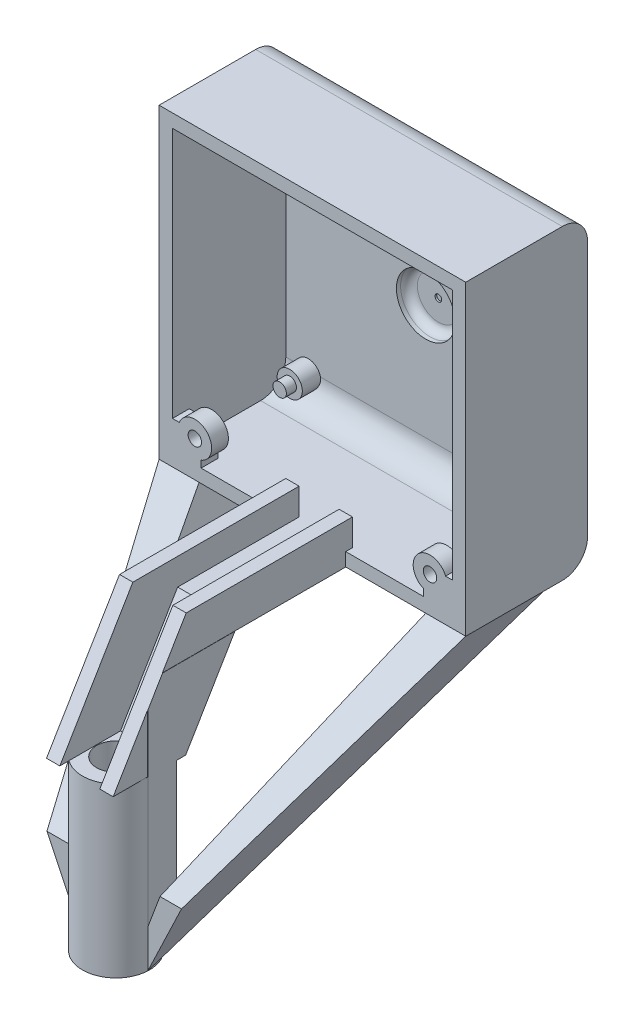
SolidWorks part; units mm, degrees
ref_plane "Front Plane" through (0, 0, 0) normal (0, 0, 1) x (1, 0, 0)
ref_plane "Top Plane" through (0, 0, 0) normal (0, 1, 0) x (1, 0, 0)
ref_plane "Right Plane" through (0, 0, 0) normal (1, 0, 0) x (0, 0, -1)
sketch "Sketch1" plane through (0, 0, 0) normal (0, 0, 1) x (1, 0, 0)
  line L0 (0, 0) -> (0, -36.5125)
  line L1 (0, -36.5125) -> (36.5125, -36.5125)
  line L2 (36.5125, -36.5125) -> (36.5125, 0)
  line L3 (36.5125, 0) -> (0, 0)
  dimension "D1" = 36.5125
extrude "Extrude1" add sketch "Sketch1" along normal blind 1
sketch "Sketch2" plane through (0, 0, 1) normal (0, 0, 1) x (1, 0, 0)
  line L0 (1.5875, -1.5875) -> (34.925, -1.5875)
  line L3 (34.925, -34.925) -> (34.925, -1.5875)
  line L4 (1.5875, -34.925) -> (1.5875, -1.5875)
  line L5 (34.925, -34.925) -> (1.5875, -34.925)
  line L6 (0, 0) -> (36.5125, 0)
  line L7 (36.5125, -36.5125) -> (36.5125, 0) construction
  line L8 (36.5125, 0) -> (0, 0) construction
  line L9 (36.5125, 0) -> (36.5125, -36.5125)
  line L10 (0, -36.5125) -> (36.5125, -36.5125) construction
  line L11 (36.5125, -36.5125) -> (0, -36.5125)
  line L12 (0, 0) -> (0, -36.5125) construction
  line L13 (0, -36.5125) -> (0, 0)
extrude "Extrude2" add sketch "Sketch2" along normal blind 13.5
fillet "Fillet7" radius 3 4 edges at (18.2562, 0, 0) (18.2562, -36.5125, 0) (18.2562, -1.5875, 1) (18.2562, -34.925, 1)
sketch "Sketch5" plane through (0, 0, 1) normal (0, 0, 1) x (1, 0, 0)
  line L0 (1.5875, -1.5875) -> (34.925, -34.925) construction
  line L1 (34.925, -1.5875) -> (1.5875, -34.925) construction
  line L2 (34.925, -34.925) -> (34.925, -1.5875) construction
  circle A0 centre (4.2562, -4.2562) radius 1.5
  circle A1 centre (32.2563, -4.2562) radius 1.5
  circle A2 centre (4.2562, -32.2563) radius 1.5
  circle A3 centre (32.2563, -32.2563) radius 1.5
  point P8 (4.2562, -32.2563)
  point P9 (18.2562, -18.2562)
  point P10 (32.2563, -32.2563)
  point P11 (4.2562, -4.2562)
  point P12 (32.2563, -4.2562)
  dimension "D1" = 14
  dimension "D2" = 14
  dimension "D3" = 14
  dimension "D4" = 14
extrude "Extrude5" add sketch "Sketch5" along normal blind 2.2
sketch "Sketch6" plane through (0, 0, 3.2) normal (0, 0, 1) x (1, 0, 0)
  circle A0 centre (4.2562, -32.2563) radius 0.8
  circle A1 centre (32.2563, -32.2563) radius 0.8
  circle A2 centre (4.2562, -4.2562) radius 0.8
  circle A3 centre (32.2563, -4.2562) radius 0.8
extrude "Extrude6" add sketch "Sketch6" along normal blind 1.2
sketch "Sketch7" plane through (0, 0, 1) normal (0, 0, 1) x (1, 0, 0)
  line L0 (0, 0) -> (36.5125, -36.5125) construction
  line L1 (36.5125, 0) -> (0, -36.5125) construction
  line L2 (0, -36.5125) -> (36.5125, -36.5125) construction
  circle A0 centre (18.2562, -18.2562) radius 4.5
  point P9 (18.2562, -18.2562)
extrude "Extrude7" add sketch "Sketch7" against normal blind 2.5
sketch "Sketch8" plane through (0, 0, 1) normal (0, 0, 1) x (1, 0, 0)
  line L0 (0, 0) -> (36.5125, -36.5125) construction
  line L1 (36.5125, 0) -> (0.5068, -36.3499) construction
  circle A0 centre (18.2562, -18.2562) radius 3.5
  point P6 (18.3431, -18.3431)
extrude "Extrude9" cut sketch "Sketch8" against normal blind 1.5
fillet "Fillet8" radius 1 1 edges at (22.7562, -18.2562, -1.5)
fillet "Fillet10" radius 1 1 edges at (21.7562, -18.2562, -0.5)
sketch "Sketch9" plane through (0, 0, -0.5) normal (0, 0, 1) x (1, 0, 0)
  circle A0 centre (18.2562, -18.2562) radius 0.4
extrude "Extrude10" cut sketch "Sketch9" against normal blind 0.2
sketch "Sketch10" plane through (0, 0, 14.5) normal (0, 0, 1) x (1, 0, 0)
  line L0 (-4.7625, -31.5125) -> (46.0375, -31.5125) construction
  line L1 (5, -15.875) -> (5, -49.2125) construction
  line L2 (31.5125, -15.875) -> (31.5125, -49.2125) construction
  line L3 (31.5125, -34.1128) -> (31.5125, -36.5126)
  line L4 (31.5125, -36.5126) -> (36.5125, -36.5125)
  line L5 (36.5125, -36.5125) -> (36.5125, -31.5125)
  line L6 (36.5125, -36.5125) -> (36.5125, 0) construction
  line L7 (36.5125, -31.5125) -> (34.1128, -31.5125)
  line L8 (2.3997, -31.5125) -> (0, -31.5125)
  line L9 (0, 0) -> (0, -36.5125) construction
  line L10 (0, -31.5125) -> (0, -36.5125)
  line L11 (0, -36.5125) -> (5, -36.5125)
  line L12 (0, -36.5125) -> (36.5125, -36.5125) construction
  line L13 (5, -36.5125) -> (5, -34.1128)
  circle A0 centre (4.2562, -32.2563) radius 2 construction
  circle A1 centre (32.2563, -32.2563) radius 2 construction
  circle A2 centre (4.2562, -32.2563) radius 0.8
  circle A3 centre (32.2563, -32.2563) radius 0.8
  arc A4 (2.3997, -31.5125) -> (5, -34.1128) centre (4.2562, -32.2563) cw
  arc A5 (34.1128, -31.5125) -> (31.5125, -34.1128) centre (32.2563, -32.2563) ccw
  dimension "D1" = 5
  dimension "D2" = 5
  dimension "D3" = 5
extrude "Extrude11" add sketch "Sketch10" against normal blind 2
sketch "Sketch11" plane through (0, 0, 14.5) normal (0, 0, 1) x (1, 0, 0)
  line L0 (14.2875, -36.5125) -> (14.2875, -31.75)
  line L1 (14.2875, -31.75) -> (15.875, -31.75)
  line L2 (22.225, -31.75) -> (22.225, -36.5125)
  line L3 (0, -36.5125) -> (31.5125, -36.5125) construction
  line L4 (22.225, -36.5125) -> (14.2875, -36.5125)
  line L5 (15.875, -31.75) -> (15.875, -33.3375)
  line L6 (20.6375, -33.3375) -> (20.6375, -34.925)
  line L7 (34.925, -34.925) -> (1.5875, -34.925) construction
  line L8 (20.6375, -34.925) -> (15.875, -34.925)
  line L9 (5, -34.925) -> (31.5125, -34.925) construction
  line L10 (15.875, -33.3375) -> (15.875, -34.925)
  line L11 (22.225, -31.75) -> (20.6375, -31.75)
  line L12 (20.6375, -31.75) -> (20.6375, -33.3375)
  point P0 (4.2562, -32.2563)
  point P1 (32.2563, -32.2563)
extrude "Extrude12" add sketch "Sketch11" along normal blind 19 and the other way blind 0.8
sketch "Sketch13" plane through (14.2875, 0, 0) normal (-1, 0, 0) x (0, 0, 1)
  line L0 (33.5, -31.75) -> (25.5, -36.5125)
  line L1 (14.5, -36.5125) -> (33.5, -36.5125) construction
  line L2 (25.5, -36.5125) -> (33.5, -36.5125)
  line L3 (33.5, -36.5125) -> (33.5, -31.75)
extrude "Extrude13" cut sketch "Sketch13" against normal through all
sketch "Sketch14" plane through (0, -38.1668, 22.7212) normal (0, -0.8593, 0.5115) x (1, 0, 0)
  line L0 (22.225, 12.5443) -> (22.225, 5.1443)
  line L1 (15.875, 12.5443) -> (14.2875, 12.5443) construction
  line L2 (14.2875, 12.5443) -> (14.2875, 3.234) construction
  line L6 (22.225, 3.234) -> (22.225, 12.5443) construction
  line L7 (22.225, 12.5443) -> (20.6375, 12.5443)
  line L8 (20.6375, 12.5443) -> (20.6375, 6.3374)
  line L9 (20.6375, 6.3374) -> (15.875, 6.3374)
  line L10 (15.875, 6.3374) -> (15.875, 12.5443) construction
  line L11 (20.6375, 6.3374) -> (15.875, 6.3374) construction
  line L12 (15.875, 6.3374) -> (15.875, 12.5443)
  line L13 (15.875, 12.5443) -> (14.2875, 12.5443)
  line L14 (22.225, 5.1443) -> (14.2875, 5.1443)
  line L15 (14.2875, 5.1443) -> (14.2875, 12.5443)
extrude "Extrude14" add sketch "Sketch14" along normal blind 17
sketch "Sketch15" plane through (14.2875, 0, 0) normal (-1, 0, 0) x (0, 0, 1)
  line L0 (42.196, -46.3575) -> (33.584, -46.3575)
  line L1 (35.8375, -50.1428) -> (27.1414, -35.5353) construction
  line L2 (33.584, -46.3575) -> (35.8375, -50.1428)
  line L3 (35.8375, -50.1428) -> (42.196, -46.3575)
extrude "Extrude15" cut sketch "Sketch15" against normal through all
sketch "Sketch16" plane through (0, -46.3575, 0) normal (0, -1, 0) x (1, 0, 0)
  line L0 (14.2875, 42.196) -> (22.225, 33.584) construction
  line L1 (14.2875, 33.584) -> (22.225, 42.196) construction
  line L2 (0, 14.5) -> (14.2875, 14.5) construction
  circle A0 centre (18.2563, 37.89) radius 2.3
  circle A1 centre (18.2563, 37.89) radius 4
  dimension "D1" = 23.39
extrude "Extrude16" add sketch "Sketch16" along normal blind 20
sketch "Sketch17" plane through (0, 0, 14.5) normal (0, 0, 1) x (1, 0, 0)
  line L0 (14.2875, -36.5125) -> (22.225, -36.5125)
  line L1 (0, -36.5125) -> (14.2875, -36.5125) construction
  line L2 (22.225, -36.5125) -> (31.5125, -36.5125) construction
  line L3 (14.2875, -34.925) -> (14.2875, -36.5125)
  line L4 (34.925, -34.925) -> (1.5875, -34.925) construction
  line L5 (22.225, -34.925) -> (14.2875, -34.925)
  line L6 (5, -34.925) -> (14.2875, -34.925) construction
  line L7 (22.225, -34.925) -> (22.225, -36.5125)
extrude "Extrude17" add sketch "Sketch17" along normal blind 13.5
sketch "Sketch18" plane through (14.2875, 0, 0) normal (-1, 0, 0) x (0, 0, 1)
  line L0 (14.5, -34.925) -> (41.275, -34.925) construction
  line L1 (0, -3) -> (0, -33.5125) construction
  line L2 (38.1, -68.2625) -> (38.1, -12.7) construction
  line L4 (33.5, -31.75) -> (38.1, -39.477) construction
  line L5 (42.196, -46.3575) -> (33.5, -31.75) construction
  line L6 (41.4234, -66.3575) -> (34.3811, -66.3575) construction
  line L7 (33.89, -66.3575) -> (41.89, -66.3575) construction
  line L8 (38.1, -39.477) -> (38.1, -66.3575)
  line L9 (38.1, -66.3575) -> (0, -31.75) construction
  line L10 (14.5, -34.925) -> (-28.575, -34.925) construction
  line L11 (38.1, -39.477) -> (35.3901, -34.925)
  line L12 (35.3901, -34.925) -> (3.4954, -34.925)
  line L13 (3.4954, -34.925) -> (38.1, -66.3575)
  point P14 (14.5, -34.925)
  point P19 (35.3901, -34.925)
  point P20 (3.4954, -34.925)
extrude "Extrude18" add sketch "Sketch18" along normal up to surface and the other way up to surface
sketch "Sketch19" plane through (0, 0, 38.1) normal (0, 0, 1) x (1, 0, 0)
  line L0 (0, -66.3575) -> (49.5504, -66.3575) construction
  line L1 (0, -39.477) -> (0, -66.3575) construction
  line L2 (0, -66.3575) -> (0, 4.7625) construction
  line L3 (0, -36.5125) -> (15.875, -36.5125) construction
  line L5 (0, -66.3575) -> (14.2618, -66.3575)
  line L6 (14.2618, -66.3575) -> (0, -36.5125)
  line L7 (0, -36.5125) -> (0, -66.3575)
  line L8 (4.7625, -36.5125) -> (14.2875, -36.5125)
  line L9 (4.7625, -36.5125) -> (14.2875, -61.9125)
  line L10 (14.2875, -36.5125) -> (14.2875, -61.9125)
  line L11 (14.2875, -31.75) -> (14.2875, -82.55) construction
  point P6 (0, -36.5125)
  point P10 (4.7625, -36.5125)
  point P21 (14.2875, -31.75)
  point P23 (14.2875, -34.925)
extrude "Extrude20" cut sketch "Sketch19" against normal up to surface up to face at (9.1162, -53.7606, 24.2319)
sketch "Sketch20" plane through (15.875, 0, 0) normal (1, 0, 0) x (0, 0, -1)
  line L0 (-34.676, -63.2474) -> (-33.89, -62.5334)
  line L1 (-5.2431, -36.5125) -> (-34.676, -63.2474) construction
  line L2 (-33.89, -46.3575) -> (-33.584, -46.3575)
  line L3 (-33.584, -46.3575) -> (-27.7232, -36.5125)
  line L4 (-27.7232, -36.5125) -> (-5.2431, -36.5125)
  line L5 (-5.2431, -36.5125) -> (-33.89, -62.5334)
  line L6 (-33.89, -66.3575) -> (-33.89, -46.3575) construction
  line L7 (-34.676, -63.2474) -> (-34.676, -46.3575)
  line L8 (-34.676, -46.3575) -> (-33.89, -46.3575)
extrude "Extrude21" cut sketch "Sketch20" against normal up to surface (1.5875 mm away) up to face at (14.2875, -33.3375, 24.0725)
sketch "Sketch21" plane through (0, 0, 0) normal (-1, 0, 0) x (0, 0, 1)
  line L0 (14.5, -36.5125) -> (48.6858, -67.5646) construction
  line L1 (38.1, -66.3575) -> (38.1, -39.477) construction
  line L2 (38.1, -57.9492) -> (38.1, -23.8125) construction
  line L3 (38.1, -57.9492) -> (38.1, -36.5125)
  line L4 (38.1, -36.5125) -> (14.5, -36.5125)
  line L5 (14.5, -36.5125) -> (38.1, -57.9492)
  point P0 (14.5, -36.5125)
  point P4 (38.1, -57.9492)
extrude "Extrude22" cut sketch "Sketch21" against normal up to surface (4.7625 mm away)
sketch "Sketch22" plane through (22.225, 0, 0) normal (1, 0, 0) x (0, 0, -1)
  line L0 (-38.1, -47.625) -> (-38.1, -71.4375) construction
  line L1 (-38.1, -61.9125) -> (-38.1, -46.3575) construction
  line L2 (-5.2431, -36.5125) -> (-38.1, -66.3575)
  line L3 (-38.1, -66.3575) -> (-38.1, -39.477)
  line L4 (-42.196, -46.3575) -> (-33.5, -31.75) construction
  line L5 (-38.1, -39.477) -> (-35.3901, -34.925)
  line L6 (-35.3901, -34.925) -> (-4, -34.925)
  line L7 (-4, -34.925) -> (-5.2431, -36.5125)
extrude "Extrude23" add sketch "Sketch22" along normal up to surface and the other way up to surface
sketch "Sketch23" plane through (0, 0, 38.1) normal (0, 0, 1) x (1, 0, 0)
  line L0 (14.2618, -61.8439) -> (60.6551, -61.8439) construction
  line L1 (22.2507, -46.3575) -> (22.2507, -66.3575) construction
  line L2 (36.5125, -36.5125) -> (20.6375, -36.5125) construction
  line L3 (22.2507, -66.3575) -> (36.5125, -66.3575)
  line L4 (36.5125, -66.3575) -> (36.5125, -36.5125)
  line L5 (36.5125, -36.5125) -> (22.2507, -66.3575)
  line L6 (22.2507, -61.8439) -> (22.2507, -36.5125)
  line L7 (22.2507, -36.5125) -> (31.75, -36.5125)
  line L8 (31.75, -36.5125) -> (22.2507, -61.8439)
  point P0 (22.2507, -66.3575)
  point P1 (36.5125, -36.5125)
  point P7 (22.2507, -61.8439)
  point P8 (0, -36.5125)
  point P12 (4.7625, -36.5125)
  point P13 (31.75, -36.5125)
  dimension "D1" = 4.7625
  dimension "D2" = 4.7625
extrude "Extrude24" cut sketch "Sketch23" against normal up to surface up to face at (27.3963, -53.7606, 24.2319)
sketch "Sketch24" plane through (36.5125, 0, 0) normal (1, 0, 0) x (0, 0, -1)
  line L0 (-14.5, -36.5125) -> (-36.3352, -36.5125)
  line L1 (-36.3352, -36.5125) -> (-38.1, -39.477)
  line L2 (-38.1, -39.477) -> (-38.1, -57.9492)
  line L3 (-38.1, -57.9492) -> (-14.5, -36.5125)
  point P0 (-14.5, -36.5125)
  point P1 (-36.3352, -36.5125)
  point P3 (-38.1, -39.477)
  point P5 (-38.1, -57.9492)
extrude "Extrude25" cut sketch "Sketch24" against normal up to surface (5.8742 mm away)
sketch "Sketch25" plane through (0, -34.925, 0) normal (0, 1, 0) x (1, 0, 0)
  line L0 (0, -14.5) -> (14.2875, -14.5)
  line L1 (14.2875, -13.7) -> (14.2875, -33.5) construction
  line L2 (14.2875, -13.7) -> (14.2875, -35.3901) construction
  line L3 (14.2875, -14.5) -> (14.2875, -42.8625)
  line L4 (14.2875, -42.8625) -> (0, -42.8625)
  line L5 (0, -42.8625) -> (0, -14.5)
  line L6 (22.225, -14.5) -> (36.5125, -14.5)
  line L7 (36.5125, -14.5) -> (0, -14.5) construction
  line L8 (22.225, -13.7) -> (22.225, -33.5) construction
  line L9 (36.5125, -14.5) -> (36.5125, -42.8625)
  line L10 (36.5125, -42.8625) -> (22.225, -42.8625)
  line L11 (22.225, -42.8625) -> (22.225, -14.5)
extrude "Extrude26" cut sketch "Sketch25" against normal up to surface (1.5875 mm away) up to face at (18.5237, -36.5125, 16.4581)
sketch "Sketch26" plane through (20.6375, 0, 0) normal (-1, 0, 0) x (0, 0, 1)
  line L0 (34.676, -46.3575) -> (33.584, -46.3575)
  line L1 (33.584, -46.3575) -> (27.7232, -36.5125)
  line L2 (27.7232, -36.5125) -> (5.2431, -36.5125)
  line L3 (34.676, -46.3575) -> (34.676, -63.2474)
  line L4 (34.676, -63.2474) -> (5.2431, -36.5125)
extrude "Extrude27" cut sketch "Sketch26" against normal up to surface (1.6132 mm away) up to face at (22.2507, -45.58, 29.0727)
